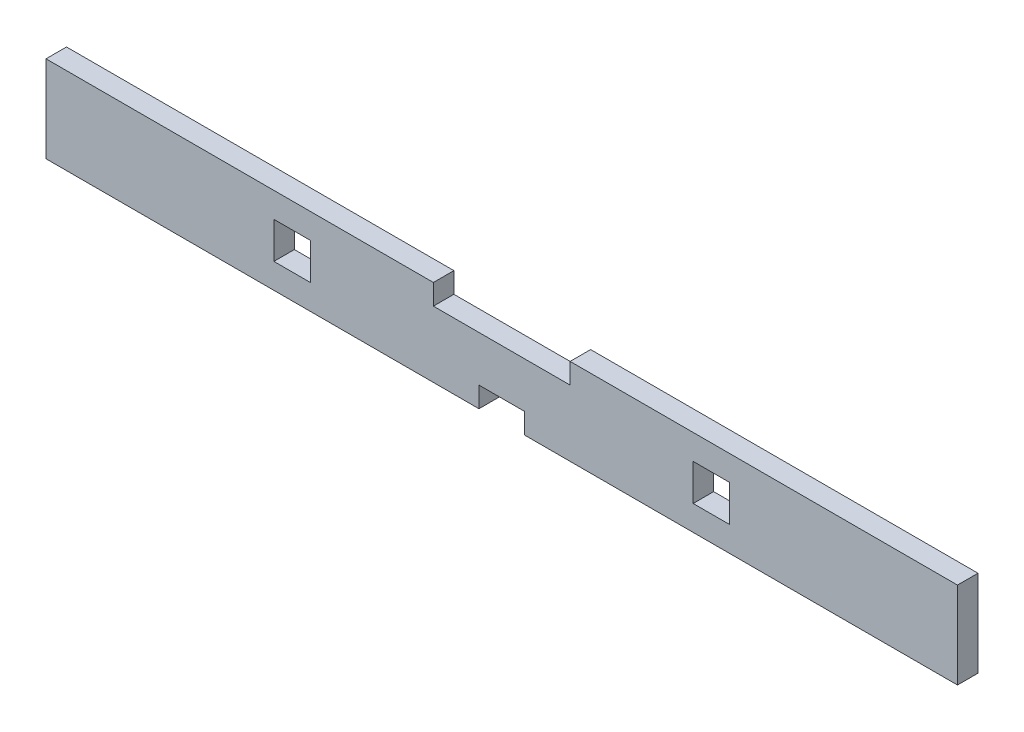
SolidWorks part; units mm, degrees
ref_plane "Front Plane" through (0, 0, 0) normal (0, 0, 1) x (1, 0, 0)
ref_plane "Top Plane" through (0, 0, 0) normal (0, 1, 0) x (1, 0, 0)
ref_plane "Right Plane" through (0, 0, 0) normal (1, 0, 0) x (0, 0, -1)
sketch "Sketch1" plane through (0, 0, 0) normal (0, 0, 1) x (1, 0, 0)
  line L1 (-127, -25.4) -> (127, -25.4)
  line L2 (-127, -25.4) -> (-127, 25.4)
  line L3 (-127, 25.4) -> (127, 25.4)
  line L4 (127, -25.4) -> (127, 25.4)
  line L5 (-127, -25.4) -> (127, 25.4) construction
  line L6 (-127, 25.4) -> (127, -25.4) construction
  point P0 (0, 0)
  dimension "D1" = 254
  dimension "D2" = 50.8
extrude "Boss-Extrude1" add sketch "Sketch1" along normal blind 5.715
sketch "Sketch2" plane through (0, 0, 5.715) normal (0, 0, 1) x (1, 0, 0)
  line L0 (-127, 25.4) -> (-127, -25.4) construction
  line L1 (-63.5, -5.08) -> (-53.34, -5.08)
  line L2 (-63.5, -5.08) -> (-63.5, 5.08)
  line L3 (-63.5, 5.08) -> (-53.34, 5.08)
  line L4 (-53.34, -5.08) -> (-53.34, 5.08)
  line L5 (-63.5, -5.08) -> (-53.34, 5.08) construction
  line L6 (-63.5, 5.08) -> (-53.34, -5.08) construction
  line L7 (53.34, -5.08) -> (63.5, -5.08)
  line L8 (53.34, -5.08) -> (53.34, 5.08)
  line L9 (53.34, 5.08) -> (63.5, 5.08)
  line L10 (63.5, -5.08) -> (63.5, 5.08)
  line L11 (53.34, -5.08) -> (63.5, 5.08) construction
  line L12 (53.34, 5.08) -> (63.5, -5.08) construction
  line L13 (127, -25.4) -> (127, 25.4) construction
  line L15 (-6.35, -12.065) -> (6.35, -12.065)
  line L16 (-6.35, -12.065) -> (-6.35, -6.35)
  line L17 (-6.35, -6.35) -> (6.35, -6.35)
  line L18 (6.35, -12.065) -> (6.35, -6.35)
  line L19 (-6.35, -12.065) -> (6.35, -6.35) construction
  line L20 (-6.35, -6.35) -> (6.35, -12.065) construction
  line L21 (-19.05, 6.35) -> (19.05, 6.35)
  line L22 (-19.05, 6.35) -> (-19.05, 12.065)
  line L23 (-19.05, 12.065) -> (19.05, 12.065)
  line L24 (19.05, 6.35) -> (19.05, 12.065)
  line L25 (-19.05, 6.35) -> (19.05, 12.065) construction
  line L26 (-19.05, 12.065) -> (19.05, 6.35) construction
  point P0 (-58.42, 0)
  point P5 (58.42, 0)
  point P15 (0, 9.2075)
  point P16 (0, -9.2075)
  dimension "D1" = 10.16
  dimension "D2" = 63.5
  dimension "D3" = 63.5
  dimension "D4" = 127
  dimension "D5" = 5.715
  dimension "D6" = 38.1
  dimension "D7" = 6.35
  dimension "D8" = 6.35
  dimension "D9" = 5.715
  dimension "D10" = 12.7
extrude "Cut-Extrude1" cut sketch "Sketch2" against normal through all
sketch "Sketch3" plane through (0, 0, 5.715) normal (0, 0, 1) x (1, 0, 0)
  line L0 (-127, -12.065) -> (127, -12.065)
  line L1 (-127, 25.4) -> (-127, -25.4) construction
  line L2 (127, -25.4) -> (127, 25.4) construction
  line L3 (-127, 12.065) -> (127, 12.065)
  line L4 (127, 12.065) -> (127, -12.065)
  line L5 (-127, -12.065) -> (-127, 12.065)
  line M9 (-19.05, 12.065) -> (19.05, 12.065)
  line M15 (6.35, -12.065) -> (-6.35, -12.065)
  line M21 (127, -25.4) -> (127, 25.4)
  line M22 (127, 25.4) -> (-127, 25.4)
  line M23 (-127, 25.4) -> (-127, -25.4)
  line M24 (-127, -25.4) -> (127, -25.4)
extrude "Cut-Extrude2" cut sketch "Sketch3" against normal through all contours L3 M23 M9 M21 M22 | L0 M23 M24 M21 M15
